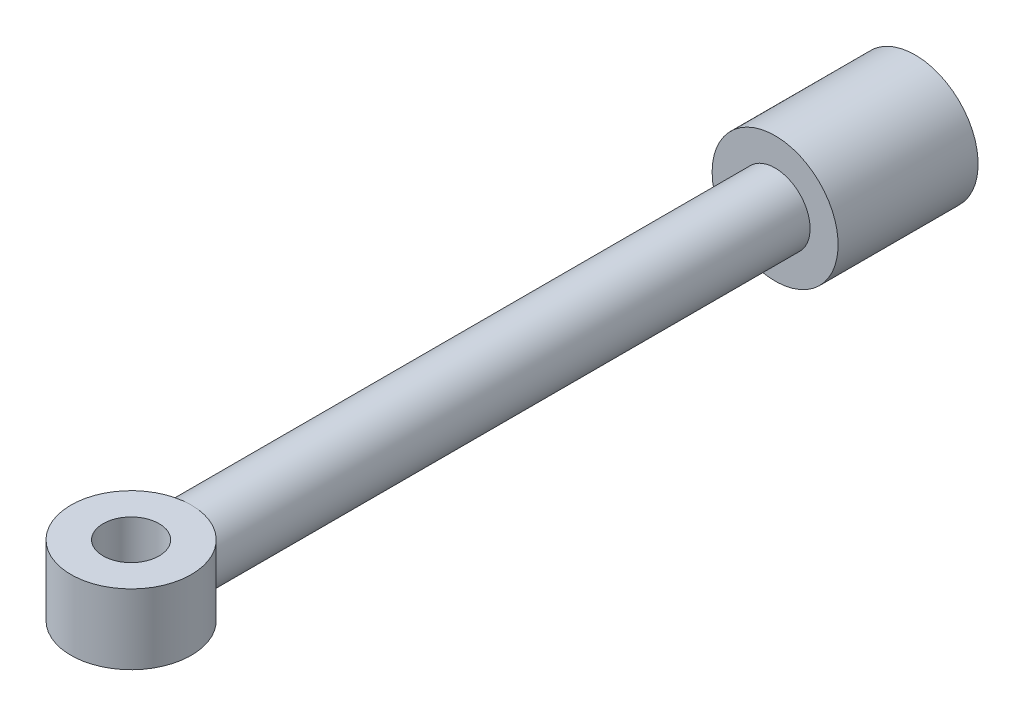
SolidWorks part; units mm, degrees
material "AISI 4340 Steel, normalized"
ref_plane "Front Plane" through (0, 0, 0) normal (0, 0, 1) x (1, 0, 0)
ref_plane "Top Plane" through (0, 0, 0) normal (0, 1, 0) x (1, 0, 0)
ref_plane "Right Plane" through (0, 0, 0) normal (1, 0, 0) x (0, 0, -1)
sketch "Sketch1" plane through (0, 0, 0) normal (0, 1, 0) x (1, 0, 0)
  line L0 (0, -75) -> (0, -635) construction
  line L1 (0, -75) -> (45, -75)
  line L4 (45, -75) -> (45, -175)
  line L5 (45, -175) -> (25, -175)
  line L6 (25, -175) -> (25, -600.0143)
  line L7 (25, -600.0143) -> (0, -600.0143)
  line L8 (0, -600.0143) -> (0, -75)
  circle A0 centre (0, -635) radius 20 construction
  circle A1 centre (0, -635) radius 43 construction
  circle A2 centre (0, 0) radius 20 construction
  dimension "D1" = 86
  dimension "D2" = 560
  dimension "D3" = 50
  dimension "D4" = 100
  dimension "D5" = 45
  dimension "D7" = 75
revolve "Revolve1" add sketch "Sketch1" angle 360 about L0
sketch "Sketch3" plane through (0, 0, 0) normal (0, 1, 0) x (1, 0, 0)
  circle A0 centre (0, -635) radius 20
  circle A1 centre (0, -635) radius 43
  circle A2 centre (0, -635) radius 43 construction
  circle A3 centre (0, -635) radius 20 construction
extrude "Boss-Extrude1" add sketch "Sketch3" along normal mid plane 50
